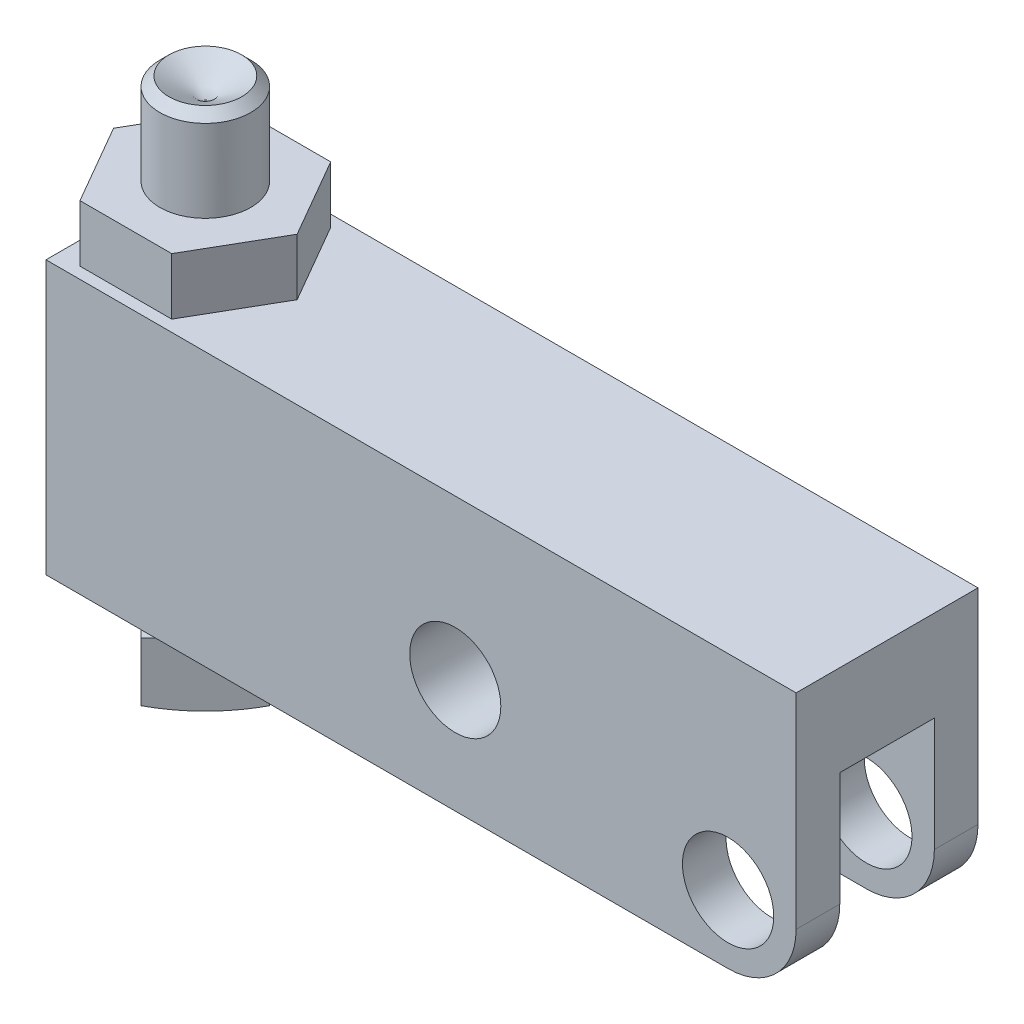
SolidWorks part; units mm, degrees
material "Alloy Steel"
ref_plane "Front Plane" through (0, 0, 0) normal (0, 0, 1) x (1, 0, 0)
ref_plane "Top Plane" through (0, 0, 0) normal (0, 1, 0) x (1, 0, 0)
ref_plane "Right Plane" through (0, 0, 0) normal (1, 0, 0) x (0, 0, -1)
sketch "Sketch11" plane through (0, 0, 0) normal (0, 0, 1) x (1, 0, 0)
  line L1 (-47.625, 14.3002) -> (4.7498, 14.3002)
  line L2 (-47.625, 14.3002) -> (-47.625, -4.7498)
  line L3 (-47.625, -4.7498) -> (4.7498, -4.7498)
  line L4 (4.7498, 14.3002) -> (4.7498, -4.7498)
  circle A0 centre (0, 0) radius 3.1877
  circle A1 centre (-19.05, 3.175) radius 3.1813
  dimension "D1" = 6.3754
  dimension "D6" = 6.3627
  dimension "D2" = 4.7498
  dimension "D3" = 47.625
  dimension "D4" = 19.05
  dimension "D5" = 19.05
  dimension "D7" = 4.7498
  dimension "D8" = 3.175
extrude "Extrude3" add sketch "Sketch11" along normal mid plane 12.7
sketch "Sketch12" plane through (0, -4.7498, 0) normal (0, -1, 0) x (1, 0, 0)
  line L0 (0, 0) -> (-16.2248, 0) construction
  line L1 (-7.9502, 3.302) -> (4.7498, 3.302)
  line L2 (4.7498, 6.35) -> (4.7498, -6.35) construction
  line L3 (4.7498, 3.302) -> (4.7498, -3.302)
  line L4 (-47.625, 6.35) -> (4.7498, 6.35) construction
  line L5 (-7.9502, -3.302) -> (4.7498, -3.302)
  arc A0 (-7.9502, 3.302) -> (-7.9502, -3.302) centre (-7.9502, 0) ccw
  dimension "D3" = 16.002
  dimension "D1" = 6.604
  dimension "D2" = 3.048
extrude "Cut-Extrude1" cut sketch "Sketch12" against normal blind 12.7
fillet "Fillet1" radius 4.7498 2 edges at (4.7498, -4.7498, -4.826) (4.7498, -4.7498, 4.826)
sketch "Sketch13" plane through (0, 14.3002, 0) normal (0, 1, 0) x (1, 0, 0)
  line L1 (-36.4413, 0) -> (-39.6456, 5.5499)
  line L2 (-39.6456, 5.5499) -> (-46.054, 5.5499)
  line L3 (-46.054, 5.5499) -> (-49.2583, 0)
  line L4 (-49.2583, 0) -> (-46.054, -5.5499)
  line L5 (-46.054, -5.5499) -> (-39.6456, -5.5499)
  line L6 (-39.6456, -5.5499) -> (-36.4413, 0)
  circle A0 centre (-42.8498, 0) radius 5.5499 construction
  dimension "D1" = 11.0998
  dimension "D2" = 42.8498
extrude "Extrude4" add sketch "Sketch13" along normal blind 3.9624
sketch "Sketch14" plane through (0, 0, 0) normal (0, 0, 1) x (1, 0, 0)
  line L0 (-42.8498, 26.5852) -> (-42.8498, -12.9942) construction
  line L1 (-36.4413, 18.2626) -> (-36.4413, 14.3002) construction
  line L2 (-49.2583, 18.2626) -> (-49.2583, 14.3002) construction
  line L3 (-42.8498, 23.1715) -> (-45.3898, 24.638)
  line L4 (-45.3898, 24.638) -> (-46.0248, 24.003)
  line L5 (-46.0248, 24.003) -> (-46.0248, -7.112)
  line L6 (-46.0248, -7.112) -> (-53.3234, -7.112)
  line L7 (-53.3234, -7.112) -> (-53.3234, -7.874)
  line L9 (-42.8498, 23.1715) -> (-42.8498, -11.8618)
  line L10 (-47.625, -4.7498) -> (0, -4.7498) construction
  arc A0 (-53.3234, -7.874) -> (-42.8498, -11.8618) centre (-42.8498, 3.8862) ccw
  dimension "D5" = 15.748
  dimension "D1" = 60
  dimension "D2" = 5.08
  dimension "D3" = 45
  dimension "D4" = 31.75
  dimension "D6" = 7.112
  dimension "D7" = 4.7498
  dimension "D8" = 0.762
  dimension "D9" = 6.35
  dimension "D10" = 42.8498
revolve "Revolve2" add sketch "Sketch14" angle 360 about L0
sketch "Sketch15" plane through (0, -7.112, 0) normal (0, 1, 0) x (1, 0, 0)
  line L0 (-38.3597, 0) -> (-47.3399, 0) construction
  line L1 (-42.8498, 4.4901) -> (-47.3399, 0)
  line L2 (-47.3399, 0) -> (-42.8498, -4.4901)
  line L3 (-42.8498, -4.4901) -> (-38.3597, 0)
  line L4 (-38.3597, 0) -> (-42.8498, 4.4901)
  circle A0 centre (-42.8498, 0) radius 3.175 construction
  circle A1 centre (-42.8498, 0) radius 10.4736 construction
  circle A2 centre (-42.8498, 0) radius 10.4736
  dimension "D1" = 6.35
extrude "Cut-Extrude2" cut sketch "Sketch15" against normal through all
